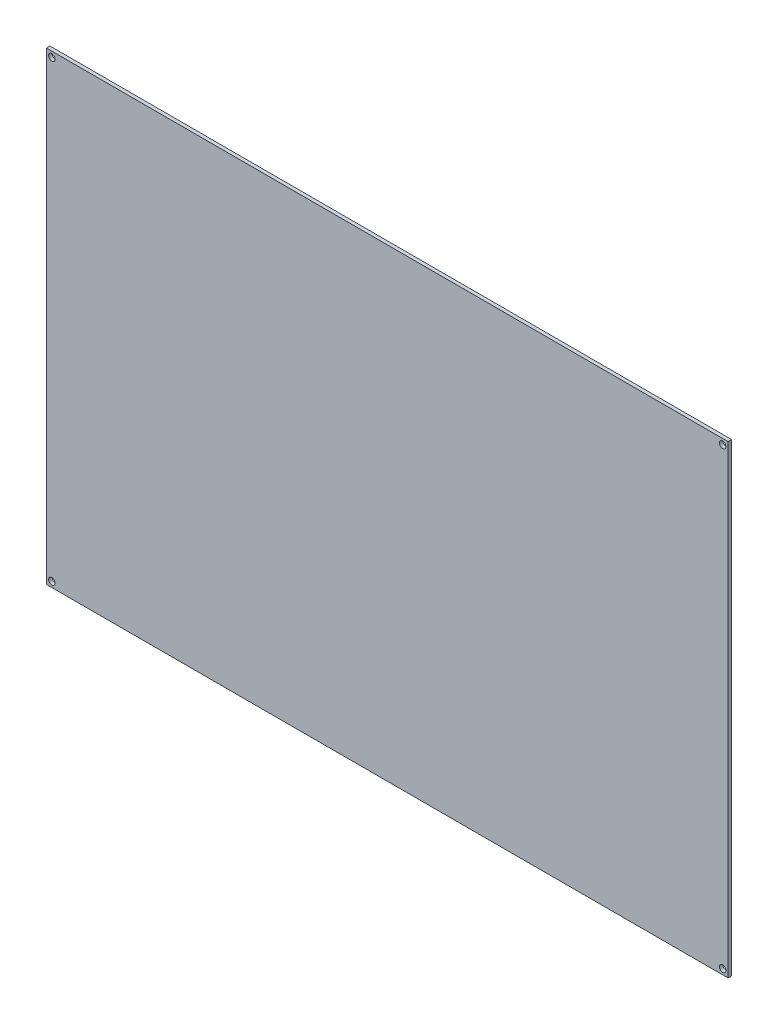
SolidWorks part; units mm, degrees
material "A-Fibra di vetro"
ref_plane "Piano frontale" through (0, 0, 0) normal (0, 0, 1) x (1, 0, 0)
ref_plane "Piano superiore" through (0, 0, 0) normal (0, 1, 0) x (1, 0, 0)
ref_plane "Piano destro" through (0, 0, 0) normal (1, 0, 0) x (0, 0, -1)
sketch "Schizzo1" plane through (0, 0, 0) normal (0, 0, 1) x (1, 0, 0)
  line L0 (314, 214) -> (0, 0) construction
  line L1 (0, 0) -> (314, 0)
  line L2 (0, 0) -> (0, 214)
  line L3 (0, 214) -> (314, 214)
  line L4 (314, 0) -> (314, 214)
  line L5 (314, 0) -> (0, 214) construction
  line L6 (157, 107) -> (157, 214) construction
  line L7 (157, 107) -> (314, 107) construction
  circle A0 centre (2.5, 211.5) radius 1.5
  circle A1 centre (311.5, 211.5) radius 1.5
  circle A2 centre (2.5, 2.5) radius 1.5
  circle A3 centre (311.5, 2.5) radius 1.5
  dimension "D4" = 104.5
  dimension "D5" = 3
  dimension "D1" = 214
  dimension "D2" = 314
  dimension "D3" = 154.5
extrude "Extrude1" add sketch "Schizzo1" against normal blind 1.6
